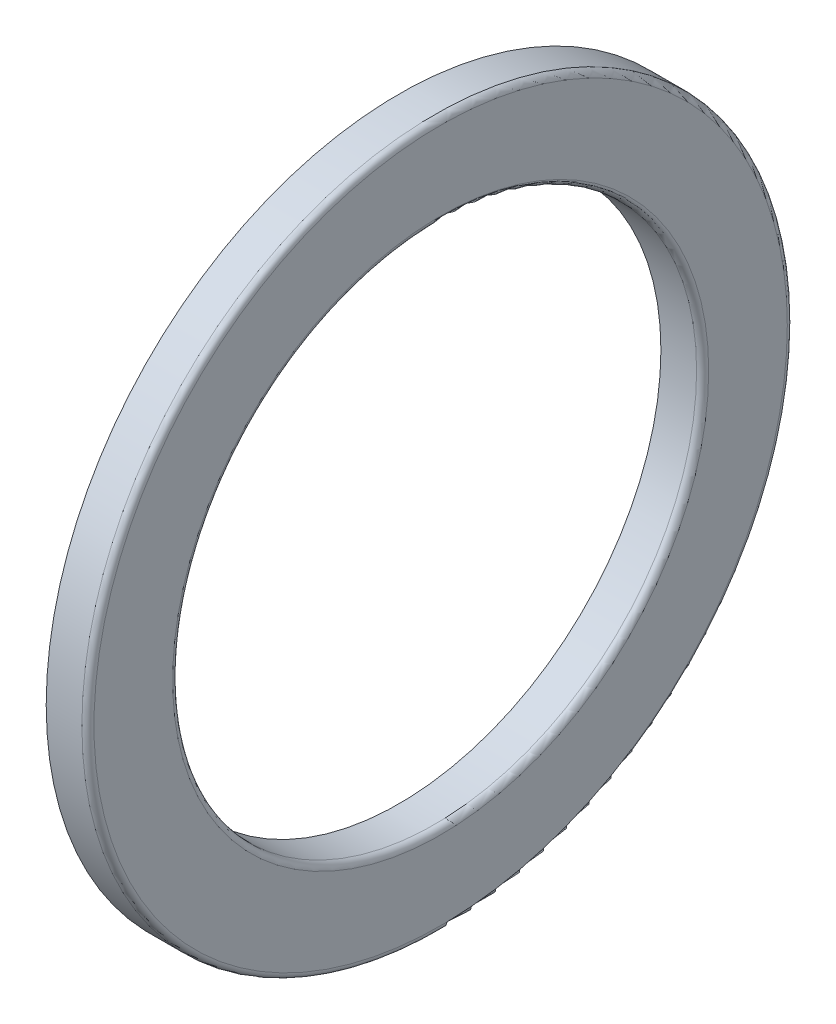
SolidWorks part; units mm, degrees
ref_plane "Alzado" through (0, 0, 0) normal (0, 0, 1) x (1, 0, 0)
ref_plane "Planta" through (0, 0, 0) normal (0, 1, 0) x (1, 0, 0)
ref_plane "Vista lateral" through (0, 0, 0) normal (1, 0, 0) x (0, 0, -1)
ref_plane "Plano1" through (0, 0, 0) normal (0, 0, 1) x (1, 0, 0)
sketch "Croquis1" plane through (0, 0, 0) normal (0, 0, 1) x (1, 0, 0)
  line L0 (9.858, 26) -> (13.4, 26)
  line L1 (14, 26.6) -> (14, 34.4)
  line L2 (13.4, 35) -> (9.858, 35)
  line L3 (9.858, 35) -> (9.858, 32.1427)
  line L4 (9.858, 27.8573) -> (9.858, 26)
  line L5 (13.4, 0) -> (9.858, 0) construction
  arc A0 (13.4, 26) -> (14, 26.6) centre (13.4, 26.6) ccw
  arc A1 (14, 34.4) -> (13.4, 35) centre (13.4, 34.4) ccw
  arc A2 (9.858, 32.1427) -> (9.858, 27.8573) centre (7, 30) cw
revolve "Revolución1" add sketch "Croquis1" angle 360 about L5
